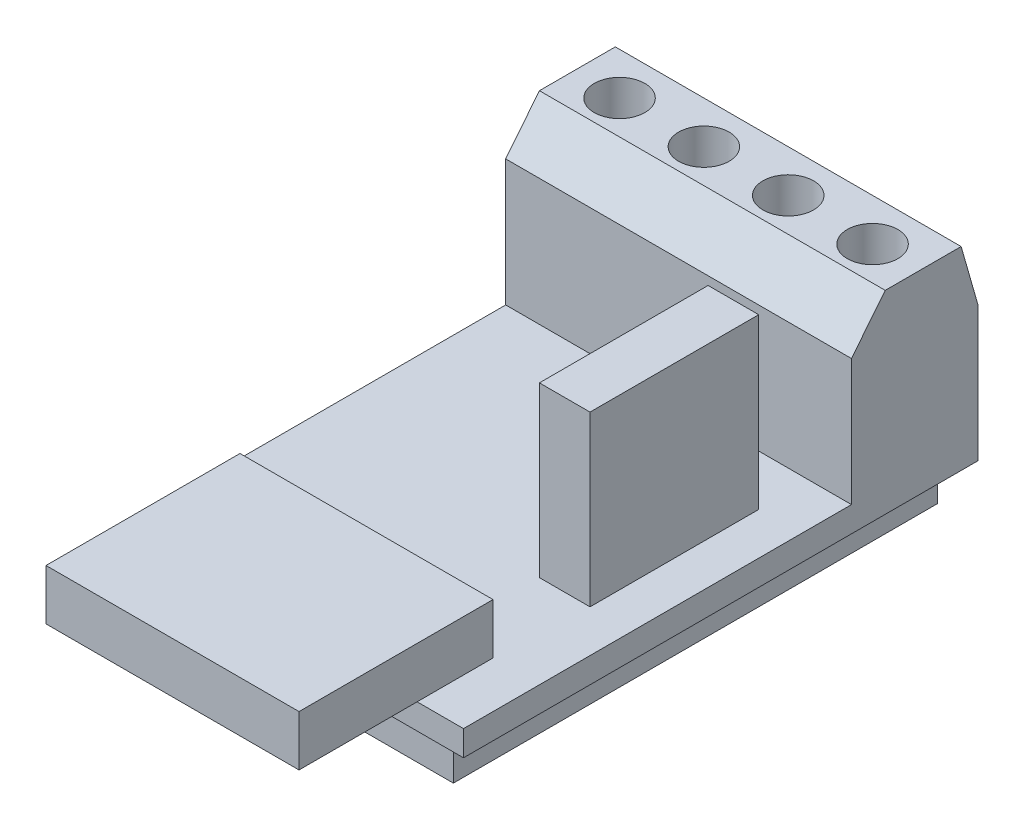
SolidWorks part; units mm, degrees
ref_plane "Front Plane" through (0, 0, 0) normal (0, 0, 1) x (1, 0, 0)
ref_plane "Top Plane" through (0, 0, 0) normal (0, 1, 0) x (1, 0, 0)
ref_plane "Right Plane" through (0, 0, 0) normal (1, 0, 0) x (0, 0, -1)
sketch "Sketch1" plane through (0, 0, 0) normal (0, 1, 0) x (1, 0, 0)
  line L1 (-10.25, -15.25) -> (10.25, -15.25)
  line L2 (-10.25, -15.25) -> (-10.25, 15.25)
  line L3 (-10.25, 15.25) -> (10.25, 15.25)
  line L4 (10.25, -15.25) -> (10.25, 15.25)
  line L5 (-10.25, -15.25) -> (10.25, 15.25) construction
  line L6 (-10.25, 15.25) -> (10.25, -15.25) construction
  point P0 (0, 0)
  dimension "D1" = 30.5
  dimension "D2" = 20.5
extrude "Boss-Extrude1" add sketch "Sketch1" along normal blind 1.5
sketch "Sketch2" plane through (0, 1.5, 0) normal (0, 1, 0) x (1, 0, 0)
  line L0 (-10.25, -15.25) -> (10.25, -15.25) construction
  line L1 (-7.5, -10.75) -> (7.5, -10.75)
  line L2 (-7.5, -10.75) -> (-7.5, -22.25)
  line L3 (-7.5, -22.25) -> (7.5, -22.25)
  line L4 (7.5, -10.75) -> (7.5, -22.25)
  line L5 (-7.5, -10.75) -> (7.5, -22.25) construction
  line L6 (-7.5, -22.25) -> (7.5, -10.75) construction
  point P0 (0, -16.5)
  dimension "D1" = 15
  dimension "D2" = 0
  dimension "D3" = 4.5
  dimension "D4" = 11.5
extrude "Boss-Extrude2" add sketch "Sketch2" along normal blind 3
sketch "Sketch3" plane through (0, 1.5, 0) normal (0, 1, 0) x (1, 0, 0)
  line L0 (10.25, -15.25) -> (10.25, 15.25) construction
  line L1 (4.75, 4.75) -> (7.75, 4.75)
  line L2 (4.75, 4.75) -> (4.75, -5.25)
  line L3 (4.75, -5.25) -> (7.75, -5.25)
  line L4 (7.75, 4.75) -> (7.75, -5.25)
  line L5 (4.75, 4.75) -> (7.75, -5.25) construction
  line L6 (4.75, -5.25) -> (7.75, 4.75) construction
  line L7 (7.5, -15.25) -> (10.25, -15.25) construction
  point P0 (6.25, -0.25)
  dimension "D1" = 10
  dimension "D2" = 3
  dimension "D3" = 2.5
  dimension "D4" = 10
extrude "Boss-Extrude3" add sketch "Sketch3" along normal blind 10
sketch "Sketch4" plane through (0, 1.5, 0) normal (0, 1, 0) x (1, 0, 0)
  line L1 (-10.25, 7.75) -> (10.25, 7.75)
  line L2 (-10.25, 7.75) -> (-10.25, 15.25)
  line L3 (-10.25, 15.25) -> (10.25, 15.25)
  line L4 (10.25, 7.75) -> (10.25, 15.25)
  line L5 (-10.25, 7.75) -> (10.25, 15.25) construction
  line L6 (-10.25, 15.25) -> (10.25, 7.75) construction
  point P0 (0, 11.5)
  dimension "D1" = 7.5
extrude "Boss-Extrude4" add sketch "Sketch4" along normal blind 10
sketch "Sketch5" plane through (0, 0, -15.25) normal (0, 0, -1) x (-1, 0, 0)
  line L0 (-10.25, 11.5) -> (-10.25, 0) construction
  line L1 (-9.75, 2.5) -> (-5.625, 2.5)
  line L2 (-9.75, 2.5) -> (-9.75, 7.5)
  line L3 (-9.75, 7.5) -> (-5.625, 7.5)
  line L4 (-5.625, 2.5) -> (-5.625, 7.5)
  line L5 (-9.75, 2.5) -> (-5.625, 7.5) construction
  line L6 (-9.75, 7.5) -> (-5.625, 2.5) construction
  line L7 (-4.625, 2.5) -> (-0.5, 2.5)
  line L8 (-4.625, 2.5) -> (-4.625, 7.5)
  line L9 (-4.625, 7.5) -> (-0.5, 7.5)
  line L10 (-0.5, 2.5) -> (-0.5, 7.5)
  line L11 (-4.625, 2.5) -> (-0.5, 7.5) construction
  line L12 (-4.625, 7.5) -> (-0.5, 2.5) construction
  line L13 (0.5, 2.5) -> (4.625, 2.5)
  line L14 (0.5, 2.5) -> (0.5, 7.5)
  line L15 (0.5, 7.5) -> (4.625, 7.5)
  line L16 (4.625, 2.5) -> (4.625, 7.5)
  line L17 (0.5, 2.5) -> (4.625, 7.5) construction
  line L18 (0.5, 7.5) -> (4.625, 2.5) construction
  line L19 (5.625, 2.5) -> (9.75, 2.5)
  line L20 (5.625, 2.5) -> (5.625, 7.5)
  line L21 (5.625, 7.5) -> (9.75, 7.5)
  line L22 (9.75, 2.5) -> (9.75, 7.5)
  line L23 (5.625, 2.5) -> (9.75, 7.5) construction
  line L24 (5.625, 7.5) -> (9.75, 2.5) construction
  line L25 (10.25, 11.5) -> (10.25, 0) construction
  line L26 (-10.25, 0) -> (10.25, 0) construction
  line L27 (-10.25, 11.5) -> (10.25, 11.5) construction
  point P0 (-7.6875, 5)
  point P5 (-2.5625, 5)
  point P10 (2.5625, 5)
  point P15 (7.6875, 5)
  point P25 (-2.9897, 4.9098)
  dimension "D1" = 0.5
  dimension "D2" = 1
  dimension "D3" = 1
  dimension "D4" = 1
  dimension "D5" = 0.5
  dimension "D6" = 4.125
  dimension "D7" = 4.125
  dimension "D8" = 4.125
  dimension "D9" = 2.5
  dimension "D10" = 2.5
  dimension "D11" = 2.5
  dimension "D12" = 2.5
  dimension "D13" = 0
  dimension "D14" = 0
  dimension "D15" = 0
  dimension "D16" = 4
extrude "Cut-Extrude1" cut sketch "Sketch5" against normal blind 3
chamfer "Chamfer1" distance 2.5 distance2 2 1 edges at (0, 11.5, -7.75)
chamfer "Chamfer2" distance 3.5 distance2 1 1 edges at (0, 11.5, -15.25)
sketch "Sketch6" plane through (0, 11.5, 0) normal (0, 1, 0) x (1, 0, 0)
  line L0 (10.25, 14.25) -> (-10.25, 14.25) construction
  line L1 (-10.25, 14.25) -> (-10.25, 9.75) construction
  circle A0 centre (-7.5, 11.75) radius 1.5
  circle A1 centre (-2.5, 11.75) radius 1.5
  circle A2 centre (2.5, 11.75) radius 1.5
  circle A3 centre (7.5, 11.75) radius 1.5
  point P12 (0, 0)
  dimension "D1" = 3
  dimension "D2" = 3
  dimension "D3" = 3
  dimension "D4" = 3
  dimension "D5" = 5
  dimension "D6" = 5
  dimension "D7" = 5
  dimension "D8" = 2.5
  dimension "D9" = 2.75
extrude "Cut-Extrude2" cut sketch "Sketch6" against normal blind 3
sketch "Sketch8" plane through (0, 0, 0) normal (0, -1, 0) x (1, 0, 0)
  line L0 (-10.25, -15.25) -> (-10.25, 15.25) construction
  line L1 (-8.75, -14.35) -> (8.75, -14.35)
  line L2 (-8.75, -14.35) -> (-8.75, 14.35)
  line L3 (-8.75, 14.35) -> (8.75, 14.35)
  line L4 (8.75, -14.35) -> (8.75, 14.35)
  line L5 (-8.75, -14.35) -> (8.75, 14.35) construction
  line L6 (-8.75, 14.35) -> (8.75, -14.35) construction
  line L8 (-10.25, 15.25) -> (10.25, 15.25) construction
  point P0 (0, 0)
  dimension "D1" = 1.5
  dimension "D2" = 0.9
extrude "Boss-Extrude5" add sketch "Sketch8" along normal blind 2.5
equation "\"D7@Sketch5\"=\"D6@Sketch5\""
equation "\"D8@Sketch5\"=\"D7@Sketch5\""
equation "\"D6@Sketch5\"=(19.5-\"D2@Sketch5\"*3)/4"
equation "\"D10@Sketch5\"=\"D9@Sketch5\""
equation "\"D11@Sketch5\"=\"D9@Sketch5\""
equation "\"D12@Sketch5\"=\"D9@Sketch5\""
equation "\"D2@Sketch6\"=\"D1@Sketch6\""
equation "\"D3@Sketch6\"=\"D2@Sketch6\""
equation "\"D4@Sketch6\"=\"D2@Sketch6\""
equation "\"D6@Sketch6\"=\"D5@Sketch6\""
equation "\"D7@Sketch6\"=\"D5@Sketch6\""
